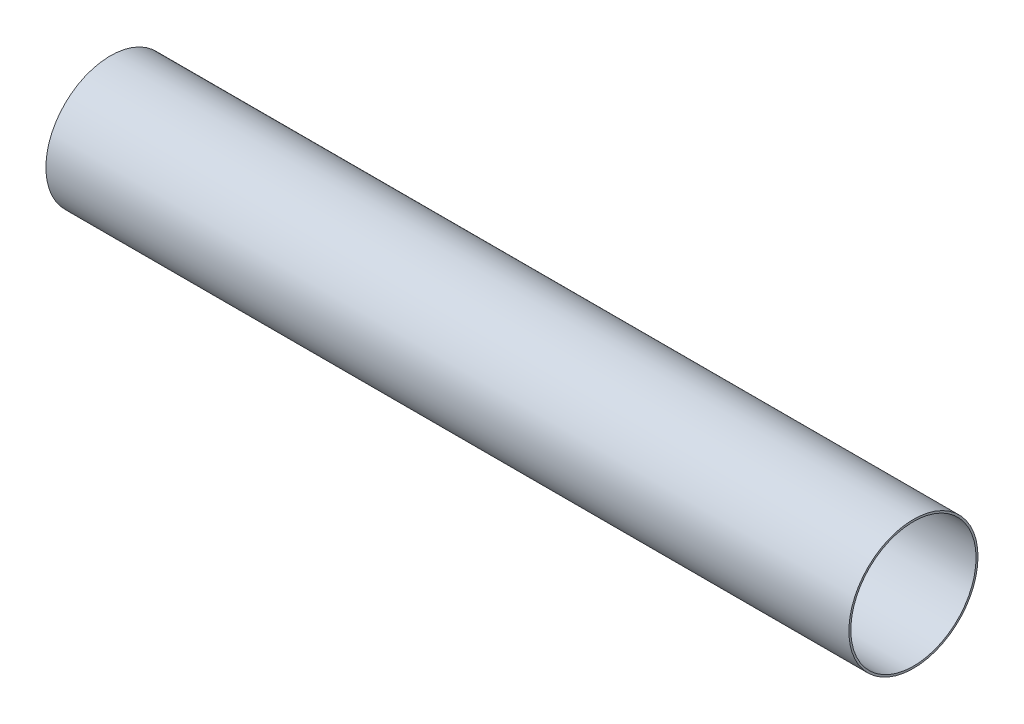
SolidWorks part; units mm, degrees
ref_plane "Front Plane" through (0, 0, 0) normal (1, 0, 0) x (0, 1, 0)
ref_plane "Top Plane" through (0, 0, 0) normal (0, 0, 1) x (0, 1, 0)
ref_plane "Right Plane" through (0, 0, 0) normal (0, 1, 0) x (-1, 0, 0)
sketch "Sketch1" plane through (0, 0, 0) normal (1, 0, 0) x (0, 1, 0)
  circle A0 centre (0, 0) radius 51.054
  circle A1 centre (0, 0) radius 49.53
  dimension "D1" = 99.06
  dimension "D2" = 102.108
extrude "Boss-Extrude1" add sketch "Sketch1" along normal blind 635
